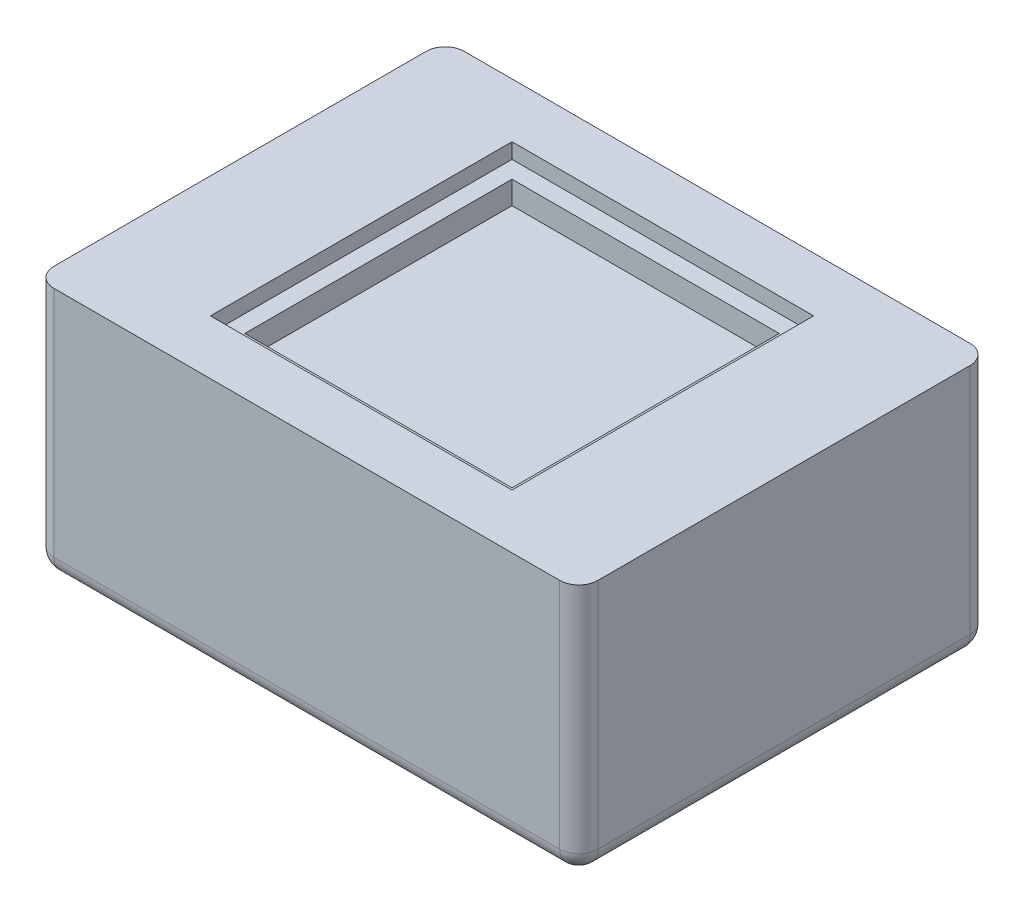
SolidWorks part; units mm, degrees
ref_plane "Front" through (0, 0, 0) normal (0, 0, 1) x (1, 0, 0)
ref_plane "Top" through (0, 0, 0) normal (0, 1, 0) x (1, 0, 0)
ref_plane "Right" through (0, 0, 0) normal (1, 0, 0) x (0, 0, -1)
sketch "草图1" plane through (0, 0, 0) normal (0, 1, 0) x (1, 0, 0)
  line L1 (-14.25, 10.75) -> (14.25, 10.75)
  line L2 (-14.25, 10.75) -> (-14.25, -10.75)
  line L3 (-14.25, -10.75) -> (14.25, -10.75)
  line L4 (14.25, 10.75) -> (14.25, -10.75)
  line L5 (-14.25, 10.75) -> (14.25, -10.75) construction
  line L6 (-14.25, -10.75) -> (14.25, 10.75) construction
  point P0 (0, 0)
  dimension "D1" = 21.5
  dimension "D2" = 28.5
extrude "凸台-拉伸1" add sketch "草图1" along normal blind 13.2
fillet "圆角1" radius 1 4 edges at (14.25, 6.6, 10.75) (-14.25, 6.6, 10.75) (-14.25, 6.6, -10.75) (14.25, 6.6, -10.75)
sketch "草图3" plane through (0, 13.2, 0) normal (0, 1, 0) x (1, 0, 0)
  line L1 (-7, 7) -> (7, 7)
  line L2 (-7, 7) -> (-7, -7)
  line L3 (-7, -7) -> (7, -7)
  line L4 (7, 7) -> (7, -7)
  line L5 (-7, 7) -> (7, -7) construction
  line L6 (-7, -7) -> (7, 7) construction
  point P0 (0, 0)
  dimension "D1" = 14
extrude "切除-拉伸2" cut sketch "草图3" against normal blind 2 contours L2 L1 L4 L3
sketch "草图4" plane through (0, 13.2, 0) normal (0, 1, 0) x (1, 0, 0)
  line L0 (-7, -7) -> (7, -7) construction
  line L1 (-7.9, 7.9) -> (7.9, 7.9)
  line L2 (-7.9, 7.9) -> (-7.9, -7.9)
  line L3 (-7.9, -7.9) -> (7.9, -7.9)
  line L4 (7.9, 7.9) -> (7.9, -7.9)
  line L5 (-7.9, 7.9) -> (7.9, -7.9) construction
  line L6 (-7.9, -7.9) -> (7.9, 7.9) construction
  point P0 (0, 0)
  dimension "D1" = 0.9
extrude "切除-拉伸3" cut sketch "草图4" against normal blind 0.8 contours L2 L1 L4 L3
fillet "圆角2" radius 1 8 edges at (0, 0, -10.75) (14.25, 0, 0) (13.9571, 0, 10.4571) (13.9571, 0, -10.4571) (-13.9571, 0, -10.4571) (-13.9571, 0, 10.4571) (0, 0, 10.75) (-14.25, 0, 0)
